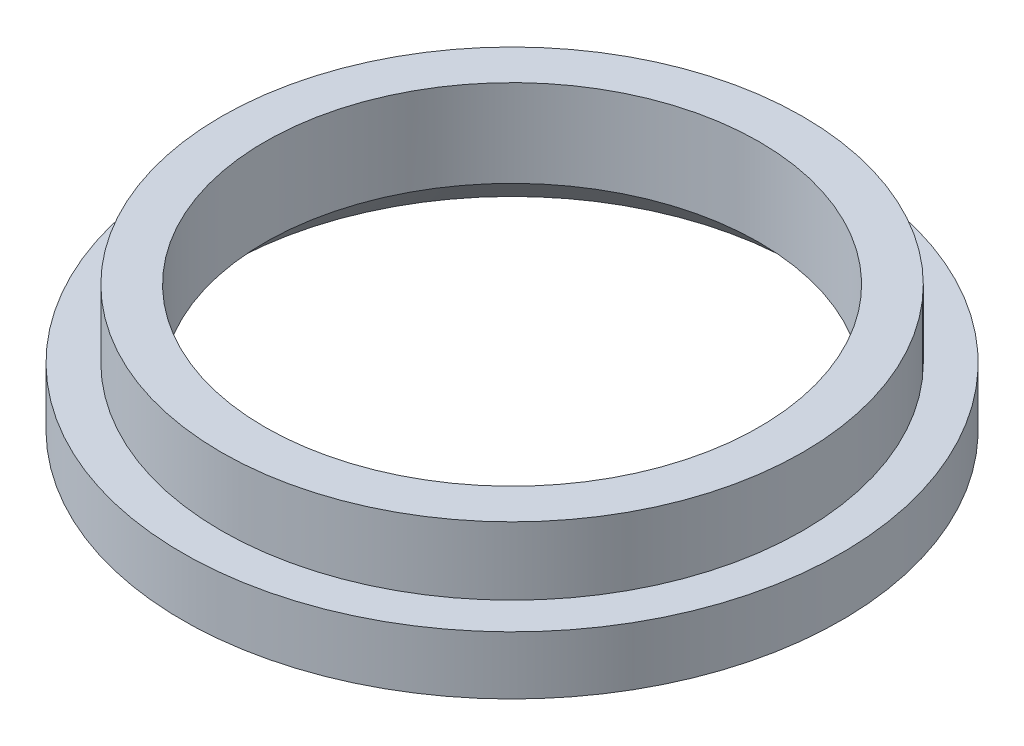
SolidWorks part; units mm, degrees
material "ABS"
ref_plane "前视基准面" through (0, 0, 0) normal (0, 0, 1) x (1, 0, 0)
ref_plane "上视基准面" through (0, 0, 0) normal (0, 1, 0) x (1, 0, 0)
ref_plane "右视基准面" through (0, 0, 0) normal (1, 0, 0) x (0, 0, -1)
sketch "草图1" plane through (0, 0, 0) normal (0, 1, 0) x (1, 0, 0)
  circle A0 centre (0, 0) radius 12.75
  circle A1 centre (0, 0) radius 15
  dimension "D1" = 25.5
  dimension "D2" = 30
extrude "凸台-拉伸1" add sketch "草图1" along normal blind 3.5
sketch "草图2" plane through (0, 0, 0) normal (0, -1, 0) x (-1, 0, 0)
  circle A0 centre (0, 0) radius 12.75
  circle A1 centre (0, 0) radius 17
  dimension "D1" = 34
extrude "凸台-拉伸2" add sketch "草图2" along normal blind 3
chamfer "倒角1" distance 2 angle 45 1 edges at (0, -3, -12.75)
